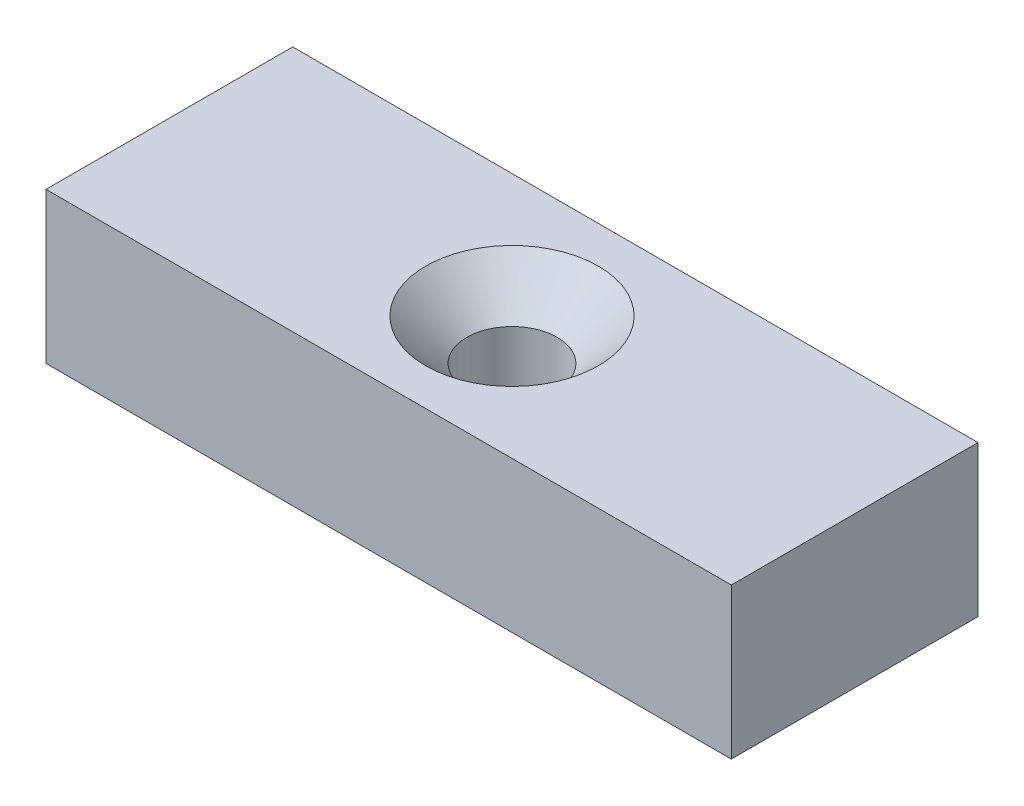
SolidWorks part; units mm, degrees
material "Plain Carbon Steel"
ref_plane "Front Plane" through (0, 0, 0) normal (0, 0, 1) x (1, 0, 0)
ref_plane "Top Plane" through (0, 0, 0) normal (0, 1, 0) x (1, 0, 0)
ref_plane "Right Plane" through (0, 0, 0) normal (1, 0, 0) x (0, 0, -1)
sketch "Sketch1" plane through (0, 0, 0) normal (0, 1, 0) x (1, 0, 0)
  line L0 (0, 0) -> (50, 0) construction
  line L1 (0, 9) -> (50, 9)
  line L2 (0, -9) -> (50, -9)
  arc A0 (0, 9) -> (0, -9) centre (0, 0) ccw
  arc A1 (50, -9) -> (50, 9) centre (50, 0) ccw
  point P3 (25, 0)
  dimension "D1" = 50
  dimension "D2" = 18
extrude "Boss-Extrude1" add sketch "Sketch1" along normal blind 11
sketch "Sketch2" plane through (0, 11, 0) normal (0, 1, 0) x (1, 0, 0)
  line L0 (50, 9) -> (0, 9) construction
  line L1 (0, 9) -> (-10.9237, 9)
  line L2 (0, 9) -> (0, -9)
  line L3 (0, -9) -> (-10.9237, -9)
  line L4 (-10.9237, 9) -> (-10.9237, -9)
  line L5 (50, 9) -> (64.3312, 9)
  line L6 (50, 9) -> (50, -9)
  line L7 (50, -9) -> (64.3312, -9)
  line L8 (64.3312, 9) -> (64.3312, -9)
  arc A0 (50, -9) -> (50, 9) centre (50, 0) ccw construction
  point P14 (25, 0)
  dimension "D1" = 18
  dimension "D2" = 18
extrude "Cut-Extrude1" cut sketch "Sketch2" against normal through all
hole_wizard "CSK for M6 Countersunk Flat Head Screw1" positions "Sketch3" profile "Sketch4" countersink size "M6" standard "ISO" end condition through all
sketch "Sketch3" plane through (0, 11, 0) normal (0, 1, 0) x (1, 0, 0)
  point P0 (25, 0)
sketch "Sketch4" plane through (25, 11, 0) normal (1, 0, 0) x (0, 0, 1)
  line L0 (0, 0) -> (0, 11)
  line L1 (0, 11) -> (3.3, 11)
  line L2 (3.3, 11) -> (3.3, 3)
  line L3 (3.3, 3) -> (6.3, 0)
  line L5 (6.3, 0) -> (0, 0)
  line L6 (-3.3, 3) -> (-6.3, 0) construction
  line L11 (0, -6.35) -> (0, 107.95) construction
  dimension "Thru Hole Dia." = 6.6
  dimension "Thru Hole Depth" = 11
  dimension "Near C'Sink Dia." = 12.6
  dimension "Near C'Sink Angle" = 90
